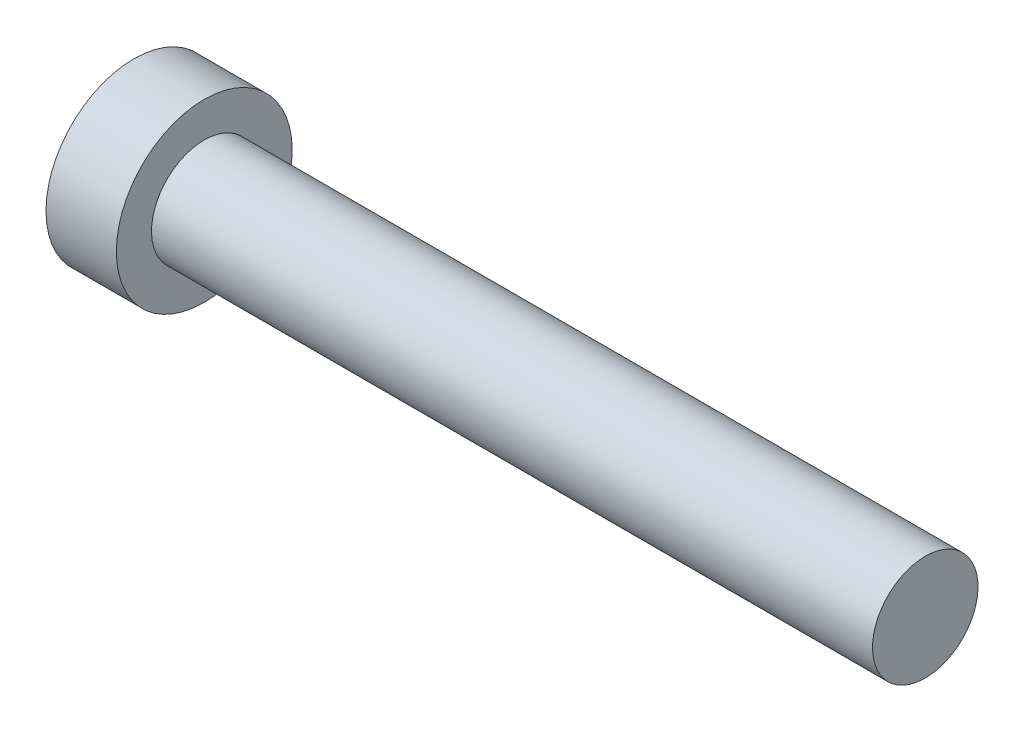
SolidWorks part; units mm, degrees
ref_plane "Plan de face" through (0, 0, 0) normal (0, 0, 1) x (1, 0, 0)
ref_plane "Plan de dessus" through (0, 0, 0) normal (0, 1, 0) x (1, 0, 0)
ref_plane "Plan de droite" through (0, 0, 0) normal (1, 0, 0) x (0, 0, -1)
sketch "Esquisse1" plane through (0, 0, 0) normal (0, 0, 1) x (1, 0, 0)
  line L0 (0, 0) -> (0, 5)
  line L1 (0, 5) -> (4, 5)
  line L2 (4, 5) -> (4, 3)
  line L3 (4, 3) -> (45, 3)
  line L4 (45, 3) -> (45, 0)
  line L5 (45, 0) -> (0, 0)
  dimension "D1" = 4
  dimension "D2" = 5
  dimension "D3" = 3
  dimension "D4" = 45
revolve "Révolution1" add sketch "Esquisse1" angle 360 about L5
